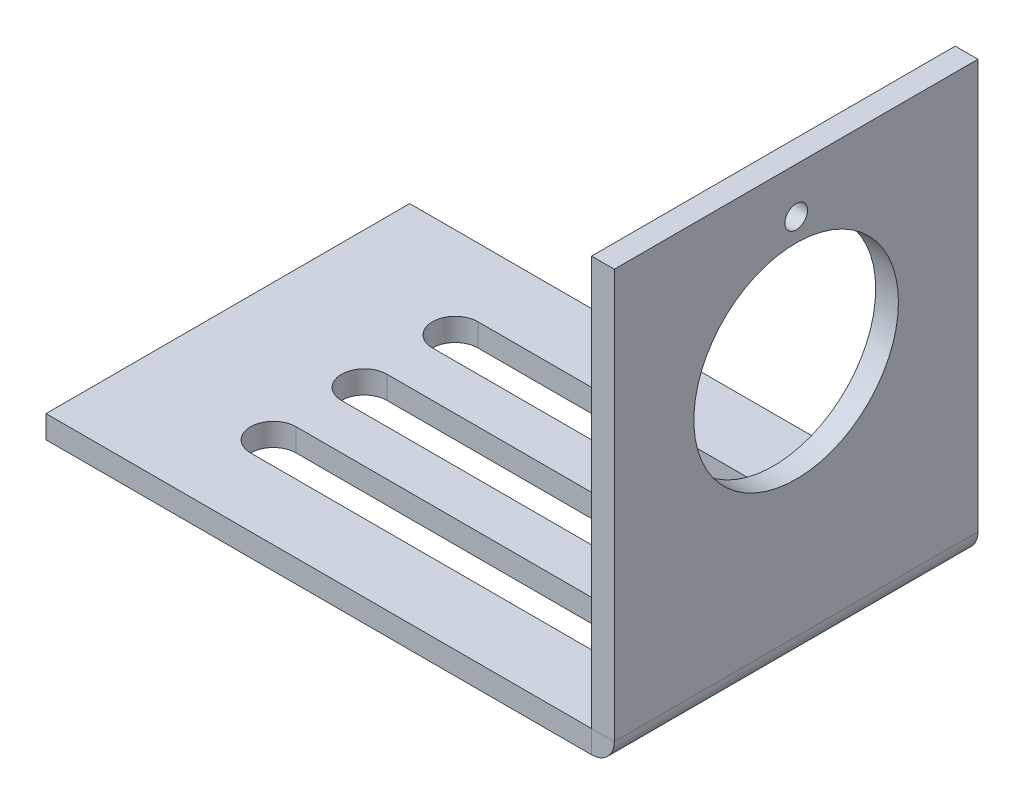
SolidWorks part; units mm, degrees
ref_plane "Front Plane" through (0, 0, 0) normal (0, 0, 1) x (1, 0, 0)
ref_plane "Top Plane" through (0, 0, 0) normal (0, 1, 0) x (1, 0, 0)
ref_plane "Right Plane" through (0, 0, 0) normal (1, 0, 0) x (0, 0, -1)
sketch "Sketch1" plane through (0, 0, 0) normal (0, 1, 0) x (1, 0, 0)
  line L1 (-19.05, -12.7) -> (19.05, -12.7)
  line L2 (-19.05, -12.7) -> (-19.05, 12.7)
  line L3 (-19.05, 12.7) -> (19.05, 12.7)
  line L4 (19.05, -12.7) -> (19.05, 12.7)
  line L5 (-19.05, -12.7) -> (19.05, 12.7) construction
  line L6 (-19.05, 12.7) -> (19.05, -12.7) construction
  point P0 (0, 0)
  dimension "D1" = 38.1
  dimension "D2" = 25.4
extrude "Boss-Extrude1" add sketch "Sketch1" along normal blind 1.5875
sketch "Sketch2" plane through (0, 0, 12.7) normal (0, 0, 1) x (1, 0, 0)
  line L1 (19.05, 1.5875) -> (20.6375, 1.5875)
  line L2 (19.05, 1.5875) -> (19.05, 30.1625)
  line L3 (19.05, 30.1625) -> (20.6375, 30.1625)
  line L4 (20.6375, 1.5875) -> (20.6375, 30.1625)
  dimension "D1" = 1.5875
  dimension "D2" = 28.575
extrude "Boss-Extrude2" add sketch "Sketch2" against normal blind 25.4 separate body
sketch "Sketch3" plane through (0, 0, 12.7) normal (0, 0, 1) x (1, 0, 0)
  line L0 (20.6375, 1.5875) -> (19.05, 1.5875)
  line L1 (19.05, 1.5875) -> (19.05, 0)
  arc A0 (19.05, 0) -> (20.6375, 1.5875) centre (19.05, 1.5875) ccw
extrude "Boss-Extrude3" add sketch "Sketch3" against normal blind 25.4 separate body
sketch "Sketch4" plane through (20.6375, 0, 0) normal (1, 0, 0) x (0, 0, -1)
  line L0 (12.7, 30.1625) -> (-12.7, 30.1625) construction
  circle A0 centre (0, 18.2563) radius 7.1438
  circle A1 centre (0, 26.9875) radius 0.7937
  point P2 (0, 30.1625)
  dimension "D1" = 14.2875
  dimension "D2" = 11.9062
  dimension "D3" = 1.5875
  dimension "D4" = 8.7312
extrude "Cut-Extrude1" cut sketch "Sketch4" against normal blind 25.4
sketch "Sketch5" plane through (0, 1.5875, 0) normal (0, 1, 0) x (1, 0, 0)
  line L0 (-9.525, -4.7625) -> (15.875, -4.7625)
  line L1 (-9.525, -7.9375) -> (15.875, -7.9375)
  line L7 (-19.05, -12.7) -> (19.05, -12.7) construction
  arc A0 (-9.525, -7.9375) -> (-9.525, -4.7625) centre (-9.525, -6.35) cw
  arc A1 (15.875, -7.9375) -> (15.875, -4.7625) centre (15.875, -6.35) ccw
  dimension "D2" = 3.175
  dimension "D1" = 25.4
  dimension "D3" = 4.7625
extrude "Cut-Extrude2" cut sketch "Sketch5" against normal blind 25.4
pattern_linear "LPattern1" count 3 spacing 6.35 along (0, 0, -1) of "Cut-Extrude2"
